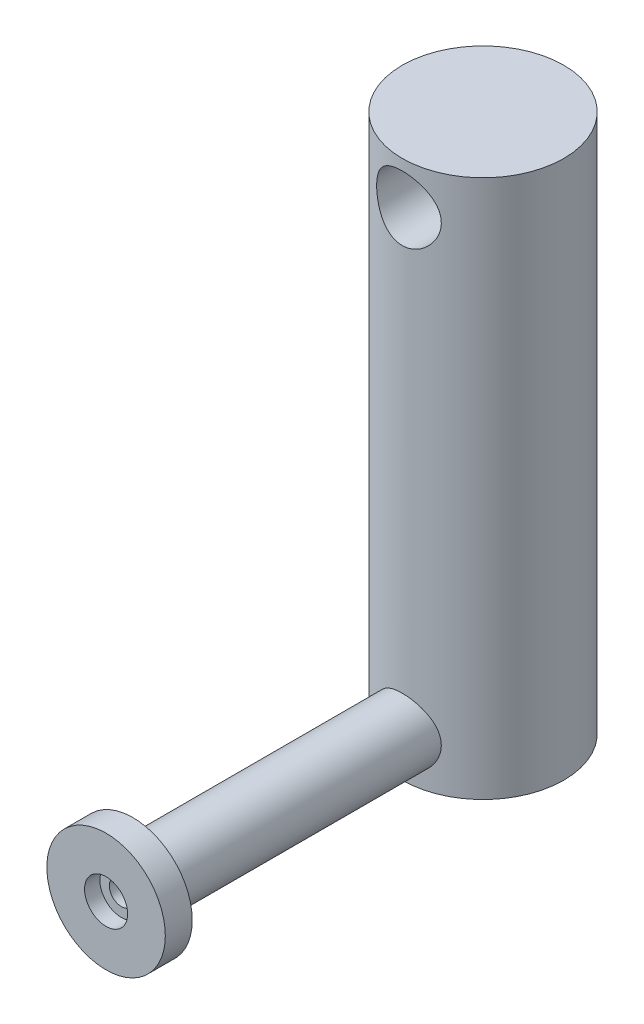
SolidWorks part; units mm, degrees
material "ABS"
ref_plane "Front Plane" through (0, 0, 0) normal (0, 0, 1) x (1, 0, 0)
ref_plane "Top Plane" through (0, 0, 0) normal (0, 1, 0) x (1, 0, 0)
ref_plane "Right Plane" through (0, 0, 0) normal (1, 0, 0) x (0, 0, -1)
sketch "Sketch1" plane through (0, 0, 0) normal (0, 1, 0) x (1, 0, 0)
  circle A0 centre (0, 0) radius 15
  dimension "D1" = 30
extrude "Boss-Extrude1" add sketch "Sketch1" along normal blind 100
ref_plane "Plane1" through (0, 0, 15) normal (0, 0, 1) x (1, 0, 0)
sketch "Sketch2" plane through (0, 0, 15) normal (0, 0, 1) x (1, 0, 0)
  circle A0 centre (0, 8) radius 6
  dimension "D1" = 12
  dimension "D2" = 8
extrude "Boss-Extrude2" add sketch "Sketch2" along normal blind 50 and the other way up to surface separate body other way up to face at (0, 100, 15)
sketch "Sketch3" plane through (0, 0, 0) normal (0, 0, 1) x (1, 0, 0)
  line L0 (15, 100) -> (-15, 100) construction
  circle A0 centre (0, 92) radius 6
  dimension "D1" = 12
  dimension "D2" = 8
extrude "Cut-Extrude1" cut sketch "Sketch3" along normal through all both and the other way through all
sketch "Sketch4" plane through (0, 0, 65) normal (0, 0, 1) x (1, 0, 0)
  circle A0 centre (0, 8) radius 11
  circle A1 centre (0, 8) radius 6 construction
  dimension "D1" = 22
extrude "Boss-Extrude3" add sketch "Sketch4" along normal blind 5
sketch "Sketch5" plane through (0, 0, 70) normal (0, 0, 1) x (1, 0, 0)
  circle A0 centre (0, 8) radius 4
  circle A1 centre (0, 8) radius 11 construction
  dimension "D1" = 8
extrude "Cut-Extrude2" cut sketch "Sketch5" against normal blind 2.85
sketch "Sketch6" plane through (0, 0, 67.15) normal (0, 0, 1) x (1, 0, 0)
  circle A0 centre (0, 8) radius 2.25
  dimension "D1" = 4.5
extrude "Cut-Extrude3" cut sketch "Sketch6" against normal blind 2.5
